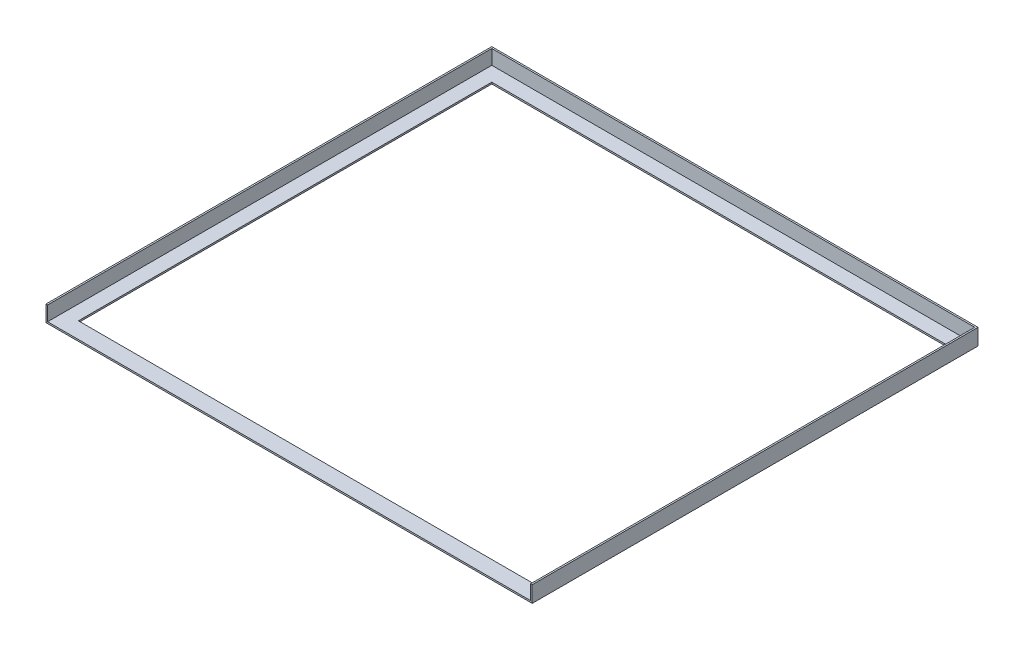
SolidWorks part; units mm, degrees
material "AISI 1020"
ref_plane "Front Plane" through (0, 0, 0) normal (0, 0, 1) x (1, 0, 0)
ref_plane "Top Plane" through (0, 0, 0) normal (0, 1, 0) x (1, 0, 0)
ref_plane "Right Plane" through (0, 0, 0) normal (1, 0, 0) x (0, 0, -1)
sketch "Sketch1" plane through (0, 0, 0) normal (0, 0, 1) x (1, 0, 0)
  line L1 (-78.9001, 15.665) -> (521.0999, 15.665)
  line L2 (-78.9001, 15.665) -> (-78.9001, -4.335)
  line L3 (-78.9001, -4.335) -> (521.0999, -4.335)
  line L4 (521.0999, 15.665) -> (521.0999, -4.335)
  dimension "D1" = 20
  dimension "D2" = 600
extrude "Boss-Extrude1" add sketch "Sketch1" against normal blind 550.1
sketch3d "3DSketch1"
  line L0 (519.0999, 15.665, -548.1) -> (-76.9001, 15.665, -548.1)
  line L1 (-76.9001, 15.665, -548.1) -> (-76.9001, 15.665, -2)
  line L2 (519.0999, 15.665, -2) -> (-76.9001, 15.665, -2)
  line L3 (519.0999, 15.665, -548.1) -> (519.0999, 15.665, -2)
  line L4 (519.0999, 15.665, -548.1) -> (-76.9001, 15.665, -548.1)
  line L5 (-76.9001, 15.665, -548.1) -> (-76.9001, 15.665, -2)
  line L6 (519.0999, 15.665, -2) -> (-76.9001, 15.665, -2)
  line L7 (519.0999, 15.665, -548.1) -> (519.0999, 15.665, -2)
  dimension "D1" = 2
extrude "Cut-Extrude1" cut sketch "3DSketch1" along direction (0, 1, 0) on the side against the normal blind 18
sketch3d "3DSketch2"
  line L0 (-58.9001, -2.335, -530.1) -> (501.0999, -2.335, -530.1)
  line L1 (-58.9001, -2.335, -20) -> (-58.9001, -2.335, -530.1)
  line L2 (501.0999, -2.335, -20) -> (-58.9001, -2.335, -20)
  line L3 (501.0999, -2.335, -530.1) -> (501.0999, -2.335, -20)
  line L4 (-58.9001, -2.335, -530.1) -> (501.0999, -2.335, -530.1)
  line L5 (-58.9001, -2.335, -20) -> (-58.9001, -2.335, -530.1)
  line L6 (501.0999, -2.335, -20) -> (-58.9001, -2.335, -20)
  line L7 (501.0999, -2.335, -530.1) -> (501.0999, -2.335, -20)
  dimension "D1" = 18
extrude "Cut-Extrude2" cut sketch "3DSketch2" along direction (0, -1, 0) on the side against the normal blind 2
sketch "Sketch2" plane through (0, 0, -2) normal (0, 0, -1) x (-1, 0, 0)
  line L1 (76.9001, 15.665) -> (-519.0999, 15.665)
  line L2 (76.9001, 15.665) -> (76.9001, -2.335)
  line L3 (76.9001, -2.335) -> (-519.0999, -2.335)
  line L4 (-519.0999, 15.665) -> (-519.0999, -2.335)
extrude "Cut-Extrude3" cut sketch "Sketch2" against normal blind 2
